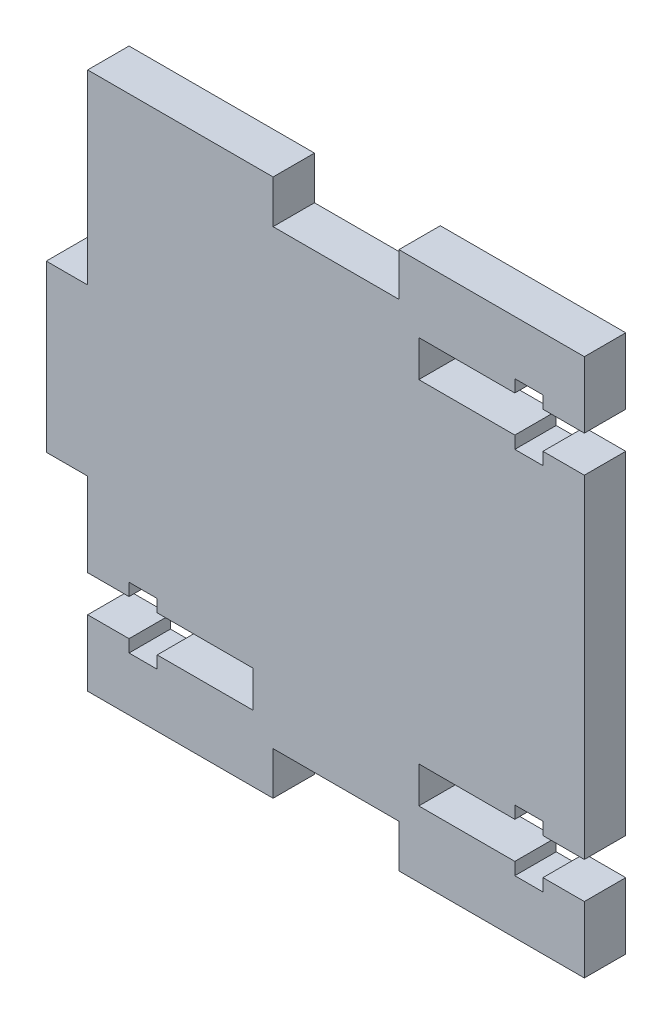
SolidWorks part; units mm, degrees
ref_plane "Front Plane" through (0, 0, 0) normal (0, 0, 1) x (1, 0, 0)
ref_plane "Top Plane" through (0, 0, 0) normal (0, 1, 0) x (1, 0, 0)
ref_plane "Right Plane" through (0, 0, 0) normal (1, 0, 0) x (0, 0, -1)
sketch "Sketch1" plane through (0, 0, 0) normal (0, 0, 1) x (1, 0, 0)
  line L1 (-30, 32.5) -> (-7.5, 32.5)
  line L2 (-30, 32.5) -> (-30, 10)
  line L3 (-30, -32.5) -> (30, -32.5)
  line L4 (30, 32.5) -> (30, -32.5)
  line L7 (-7.5, 32.5) -> (30, 32.5)
  line L8 (-30, -10) -> (-30, -32.5)
  line L9 (-30, 10) -> (-35, 10)
  line L11 (-30, -10) -> (-35, -10)
  line L12 (-35, 10) -> (-35, -10)
  dimension "D1" = 60
  dimension "D2" = 65
  dimension "D3" = 30
  dimension "D4" = 32.5
  dimension "D5" = 5
  dimension "D6" = 22.5
  dimension "D7" = 20
extrude "Boss-Extrude1" add sketch "Sketch1" along normal blind 5
sketch "Sketch3" plane through (0, 0, 5) normal (0, 0, 1) x (1, 0, 0)
  line L0 (0, 0) -> (28.1265, 0) construction
  line L13 (30, -32.5) -> (30, 32.5) construction
  line L14 (30, 24.5) -> (25, 24.5)
  line L15 (25, 24.5) -> (25, 26)
  line L16 (25, 26) -> (21.6, 26)
  line L17 (21.6, 26) -> (21.6, 24.5)
  line L18 (21.6, 24.5) -> (10, 24.5)
  line L19 (10, 24.5) -> (10, 20.1)
  line L20 (10, 20.1) -> (21.6, 20.1)
  line L21 (21.6, 20.1) -> (21.6, 18.6)
  line L22 (21.6, 18.6) -> (25, 18.6)
  line L23 (25, 18.6) -> (25, 20.1)
  line L24 (25, 20.1) -> (30, 20.1)
  line L25 (30, 24.5) -> (30, 20.1)
  line L26 (30, 32.5) -> (-30, 32.5) construction
  line L27 (0, 0) -> (0, 42.4523) construction
  line L28 (30, -24.5) -> (30, -20.1)
  line L29 (25, -20.1) -> (30, -20.1)
  line L30 (25, -18.6) -> (25, -20.1)
  line L31 (21.6, -18.6) -> (25, -18.6)
  line L32 (21.6, -20.1) -> (21.6, -18.6)
  line L33 (10, -20.1) -> (21.6, -20.1)
  line L34 (10, -24.5) -> (10, -20.1)
  line L35 (21.6, -24.5) -> (10, -24.5)
  line L36 (21.6, -26) -> (21.6, -24.5)
  line L37 (25, -26) -> (21.6, -26)
  line L38 (25, -24.5) -> (25, -26)
  line L39 (30, -24.5) -> (25, -24.5)
  line L40 (-30, -24.5) -> (-25, -24.5)
  line L41 (-25, -24.5) -> (-25, -26)
  line L42 (-25, -26) -> (-21.6, -26)
  line L43 (-21.6, -26) -> (-21.6, -24.5)
  line L44 (-21.6, -24.5) -> (-10, -24.5)
  line L45 (-10, -24.5) -> (-10, -20.1)
  line L46 (-10, -20.1) -> (-21.6, -20.1)
  line L47 (-21.6, -20.1) -> (-21.6, -18.6)
  line L48 (-21.6, -18.6) -> (-25, -18.6)
  line L49 (-25, -18.6) -> (-25, -20.1)
  line L50 (-25, -20.1) -> (-30, -20.1)
  line L51 (-30, -24.5) -> (-30, -20.1)
  dimension "D8" = 4.4
  dimension "D9" = 1.5
  dimension "D10" = 1.5
  dimension "D11" = 3.4
  dimension "D12" = 5
  dimension "D13" = 8
  dimension "D14" = 20
extrude "Cut-Extrude1" cut sketch "Sketch3" against normal blind 5
sketch "Sketch4" plane through (0, 0, 5) normal (0, 0, 1) x (1, 0, 0)
  line L1 (7.6, -32.5) -> (7.6, -27.3)
  line L3 (7.6, -27.3) -> (-7.6, -27.3)
  line L4 (-7.6, -27.3) -> (-7.6, -32.5)
  line L5 (-30, -32.5) -> (30, -32.5) construction
  line L6 (-7.6, -32.5) -> (7.6, -32.5)
  line L7 (30, -32.5) -> (30, -24.5) construction
  line L9 (0, 0) -> (24.7904, 0) construction
  line L10 (-7.6, 32.5) -> (7.6, 32.5)
  line L11 (-7.6, 27.3) -> (-7.6, 32.5)
  line L12 (7.6, 27.3) -> (-7.6, 27.3)
  line L13 (7.6, 32.5) -> (7.6, 27.3)
  dimension "D1" = 5.2
  dimension "D2" = 15.2
  dimension "D3" = 22.4
extrude "Cut-Extrude2" cut sketch "Sketch4" against normal blind 10
